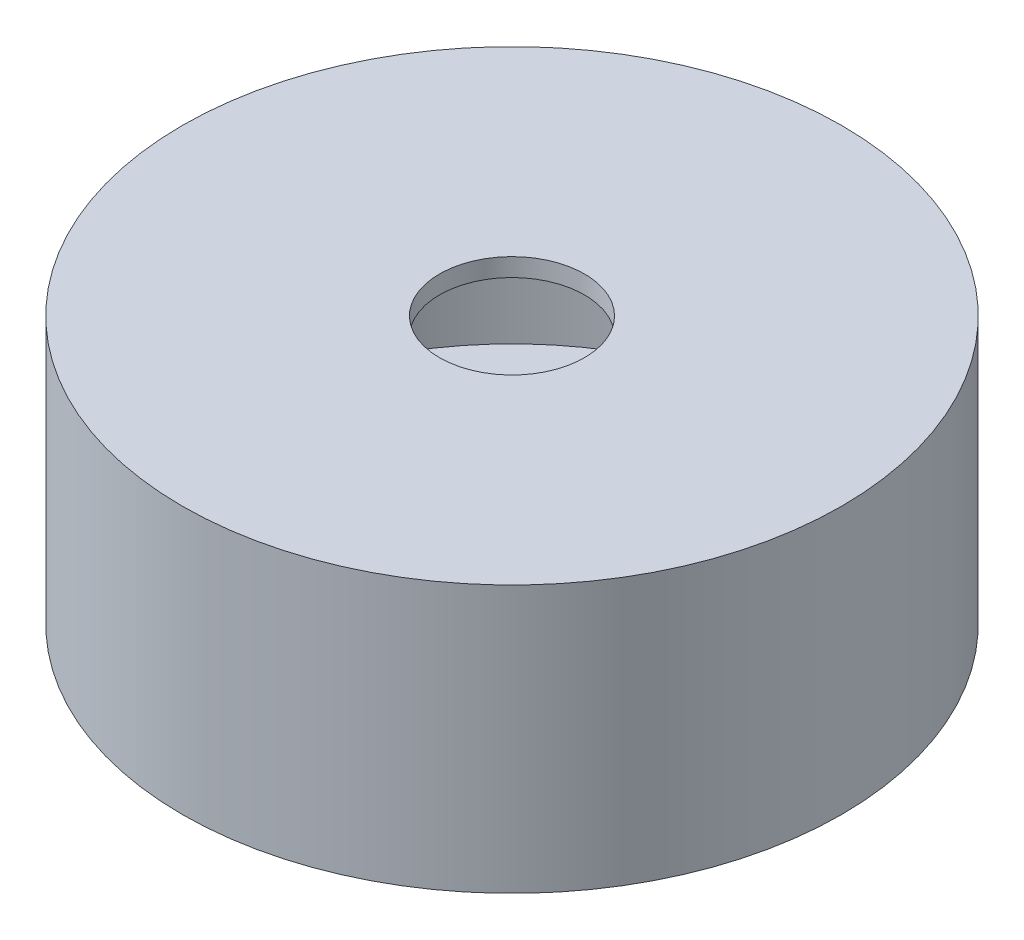
SolidWorks part; units mm, degrees
material "Cast Alloy Steel"
ref_plane "Front Plane" through (0, 0, 0) normal (0, 0, 1) x (1, 0, 0)
ref_plane "Top Plane" through (0, 0, 0) normal (0, 1, 0) x (1, 0, 0)
ref_plane "Right Plane" through (0, 0, 0) normal (1, 0, 0) x (0, 0, -1)
sketch "Sketch1" plane through (0, 0, 0) normal (0, 1, 0) x (1, 0, 0)
  line L1 (0, 0) -> (60, 0)
  line L2 (0, 0) -> (0, 40)
  line L3 (0, 40) -> (60, 40)
  line L4 (60, 0) -> (60, 40)
  line L5 (5, 7.8) -> (50, 7.8)
  line L6 (5, 7.8) -> (5, 32.2)
  line L7 (5, 32.2) -> (50, 32.2)
  line L8 (50, 7.8) -> (50, 32.2)
  circle A0 centre (17, 20) radius 50
  point P9 (5, 20)
  point P10 (0, 20)
  dimension "D6" = 100
  dimension "D1" = 40
  dimension "D2" = 60
  dimension "D3" = 45
  dimension "D4" = 24.4
  dimension "D5" = 5
  dimension "D7" = 12
extrude "Boss-Extrude1" add sketch "Sketch1" along normal blind 5 contours A0 L4 L1 L2 L3 | L1 L4 L3 L2 L8 L5 L6 L7
sketch "Sketch8" plane through (0, 0, 0) normal (0, -1, 0) x (-1, 0, 0)
  line L0 (-1060, 20) -> (48940, 20) construction
  circle A0 centre (-52.8, 28.5) radius 1.025
  circle A1 centre (-46.5, 35) radius 1.025
  circle A2 centre (-29.5, 35) radius 1.025
  circle A3 centre (-12.5, 35) radius 1.025
  circle A5 centre (-12.5, 5) radius 1.025
  circle A6 centre (-29.5, 5) radius 1.025
  circle A7 centre (-46.5, 5) radius 1.025
  circle A8 centre (-52.8, 11.5) radius 1.025
extrude "Cut-Extrude1" cut sketch "Sketch8" against normal up to next
sketch "Sketch9" plane through (0, 5, 0) normal (0, 1, 0) x (1, 0, 0)
  circle A0 centre (17, 20) radius 50
  dimension "D1" = 100
extrude "Boss-Extrude2" add sketch "Sketch9" along normal blind 32.75
sketch "Sketch10" plane through (0, 37.75, 0) normal (0, 1, 0) x (1, 0, 0)
  circle A0 centre (17, 20) radius 45
  circle A1 centre (17, 20) radius 50 construction
  dimension "D1" = 90
extrude "Cut-Extrude2" cut sketch "Sketch10" against normal blind 32.75
sketch "Sketch11" plane through (0, 37.75, 0) normal (0, 1, 0) x (1, 0, 0)
  circle A0 centre (17, 20) radius 50
  circle A1 centre (17, 20) radius 45 construction
  circle A2 centre (17, 20) radius 50 construction
extrude "Boss-Extrude3" add sketch "Sketch11" along normal blind 2.75
sketch "Sketch12" plane through (0, 40.5, 0) normal (0, 1, 0) x (1, 0, 0)
  circle A0 centre (17, 20) radius 11
  circle A1 centre (17, 20) radius 50 construction
  dimension "D1" = 22
extrude "Cut-Extrude3" cut sketch "Sketch12" against normal blind 2.75
